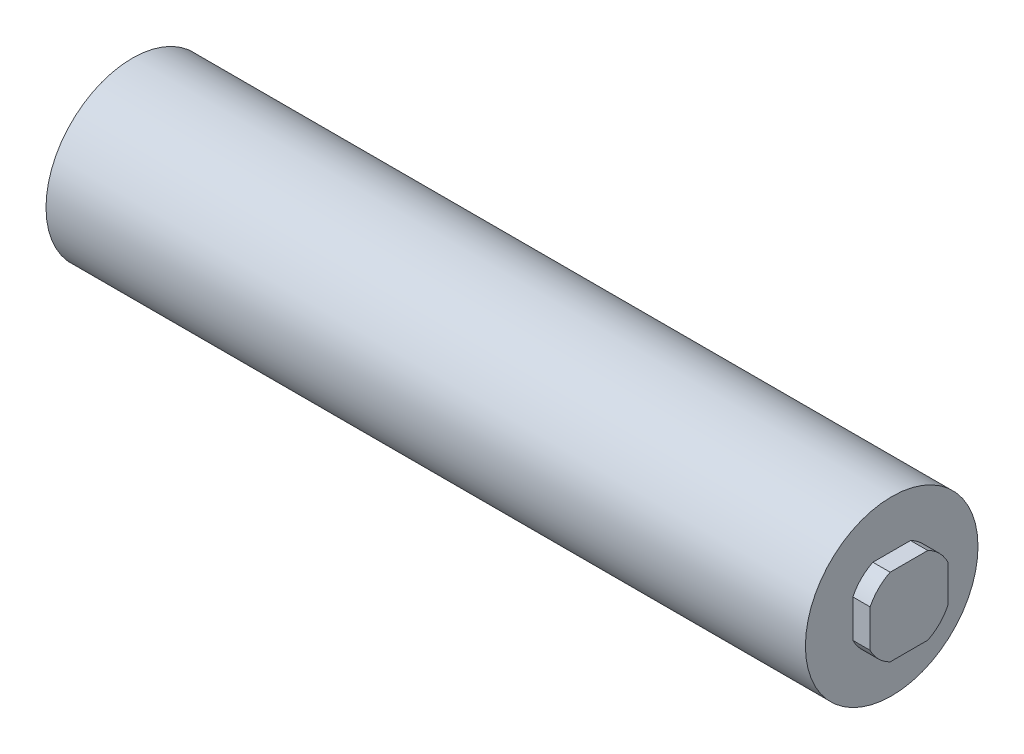
SolidWorks part; units mm, degrees
ref_plane "Front Plane" through (0, 0, 0) normal (0, 0, 1) x (1, 0, 0)
ref_plane "Top Plane" through (0, 0, 0) normal (0, 1, 0) x (1, 0, 0)
ref_plane "Right Plane" through (0, 0, 0) normal (1, 0, 0) x (0, 0, -1)
sketch "Sketch1" plane through (0, 0, 0) normal (1, 0, 0) x (0, 0, -1)
  circle A0 centre (0, 0) radius 5
  dimension "D1" = 10
extrude "Boss-Extrude1" add sketch "Sketch1" along normal blind 44
sketch "Sketch2" plane through (44, 0, 0) normal (1, 0, 0) x (0, 0, -1)
  circle A0 centre (0, 0) radius 2.5
  dimension "D1" = 5
extrude "Boss-Extrude2" add sketch "Sketch2" along normal blind 1
sketch "Sketch3" plane through (45, 0, 0) normal (1, 0, 0) x (0, 0, -1)
  line L1 (-2.25, -2.25) -> (2.25, -2.25)
  line L2 (-2.25, -2.25) -> (-2.25, 2.25)
  line L3 (-2.25, 2.25) -> (2.25, 2.25)
  line L4 (2.25, -2.25) -> (2.25, 2.25)
  line L5 (-2.25, -2.25) -> (2.25, 2.25) construction
  line L6 (-2.25, 2.25) -> (2.25, -2.25) construction
  point P0 (0, 0)
  dimension "D1" = 4.5
  dimension "D2" = 4.5
extrude "Cut-Extrude1" cut sketch "Sketch3" against normal up to surface (1 mm away) flip side to cut up to face at (44, 0, -2.5)
